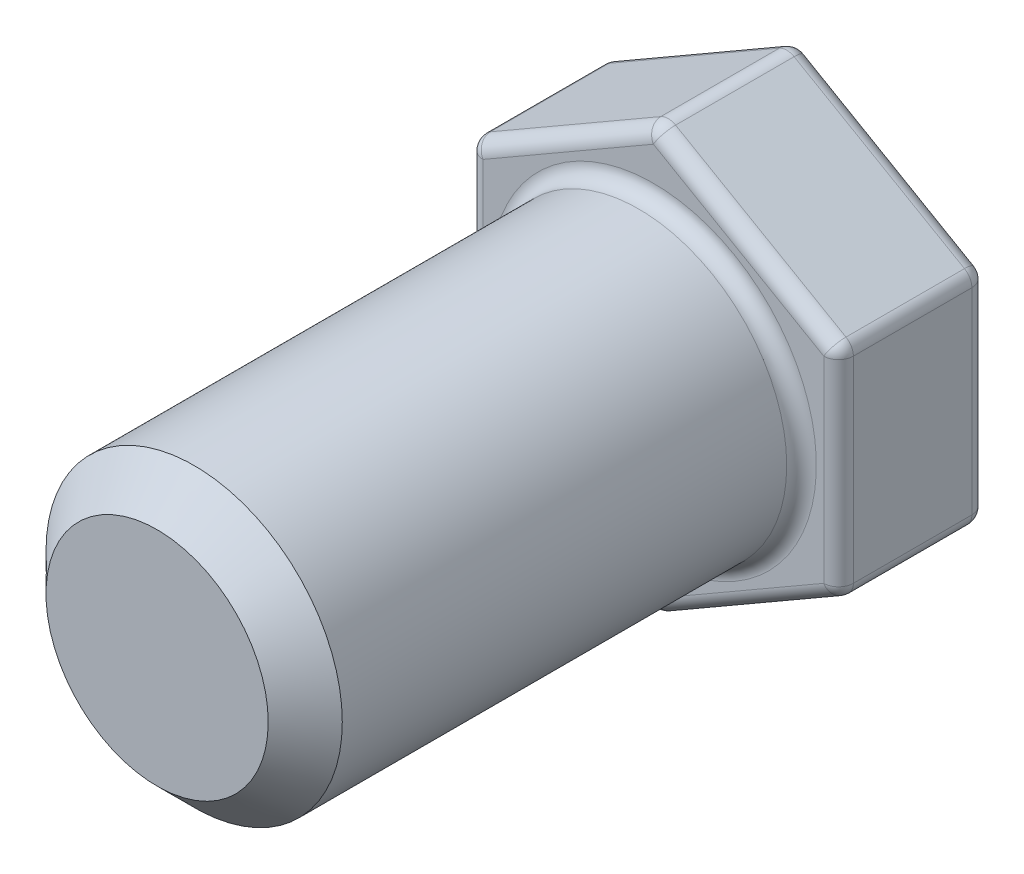
SolidWorks part; units mm, degrees
ref_plane "Front Plane" through (0, 0, 0) normal (0, 0, 1) x (1, 0, 0)
ref_plane "Top Plane" through (0, 0, 0) normal (0, 1, 0) x (1, 0, 0)
ref_plane "Right Plane" through (0, 0, 0) normal (1, 0, 0) x (0, 0, -1)
sketch "Sketch1" plane through (0, 0, 0) normal (0, 0, 1) x (1, 0, 0)
  circle A0 centre (0, 0) radius 2
  dimension "D1" = 4
extrude "Boss-Extrude1" add sketch "Sketch1" along normal blind 6.7
sketch "Sketch2" plane through (0, 0, 0) normal (0, 0, -1) x (-1, 0, 0)
  line L1 (-2.5, 1.4434) -> (-2.5, -1.4434)
  line L2 (-2.5, -1.4434) -> (0, -2.8868)
  line L3 (0, -2.8868) -> (2.5, -1.4434)
  line L4 (2.5, -1.4434) -> (2.5, 1.4434)
  line L5 (2.5, 1.4434) -> (0, 2.8868)
  line L6 (0, 2.8868) -> (-2.5, 1.4434)
  circle A0 centre (0, 0) radius 2.5 construction
  dimension "D1" = 5
extrude "Boss-Extrude2" add sketch "Sketch2" along normal blind 2
fillet "Fillet1" radius 0.2 13 edges at (-1.25, 2.1651, -2) (-2.5, 0, -2) (-1.25, -2.1651, -2) (1.25, -2.1651, -2) (2.5, 0, -2) (1.25, 2.1651, -2) (2.5, 0, 0) (1.25, -2.1651, 0) (-1.25, -2.1651, 0) (-2.5, 0, 0) (-1.25, 2.1651, 0) (1.25, 2.1651, 0) (2, 0, 0)
fillet "Fillet2" radius 0.2 18 edges at (0, 2.8191, -1.9414) (0, 2.8191, -0.0586) (-2.4414, 1.4096, -1.9414) (-2.4414, 1.4096, -0.0586) (-2.4414, -1.4096, -1.9414) (-2.4414, -1.4096, -0.0586) (0, -2.8191, -1.9414) (0, -2.8191, -0.0586) (2.4414, -1.4096, -1.9414) (2.4414, -1.4096, -0.0586) (2.4414, 1.4096, -1.9414) (2.4414, 1.4096, -0.0586) (0, 2.8868, -1) (-2.5, 1.4434, -1) (-2.5, -1.4434, -1) (0, -2.8868, -1) (2.5, -1.4434, -1) (2.5, 1.4434, -1)
chamfer "Chamfer1" distance 0.5 angle 45 1 edges at (2, 0, 6.7)
